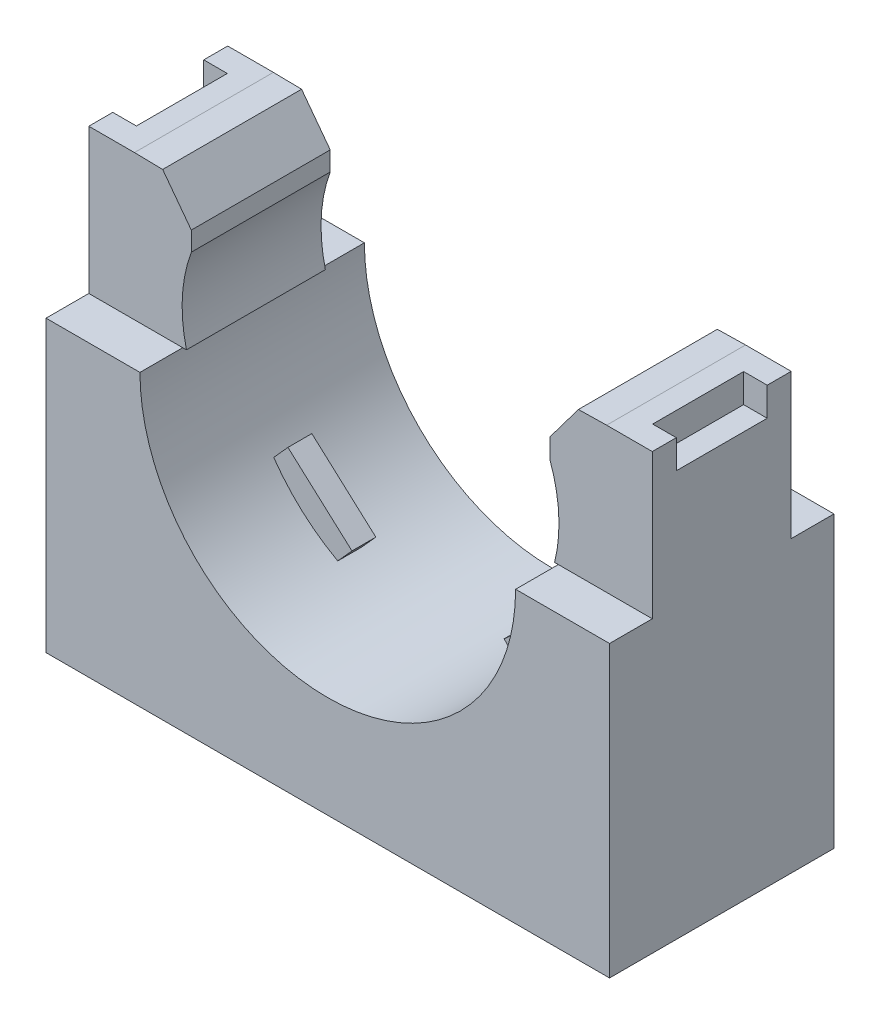
SolidWorks part; units mm, degrees
ref_plane "Front Plane" through (0, 0, 0) normal (0, 0, 1) x (1, 0, 0)
ref_plane "Top Plane" through (0, 0, 0) normal (0, 1, 0) x (1, 0, 0)
ref_plane "Right Plane" through (0, 0, 0) normal (1, 0, 0) x (0, 0, -1)
sketch "Sketch1" plane through (0, 0, 0) normal (0, 0, 1) x (1, 0, 0)
  line L0 (-14.986, -11.557) -> (14.986, 11.557) construction
  line L1 (-14.986, 11.557) -> (14.986, 11.557)
  line L2 (-14.986, 11.557) -> (-14.986, -11.557)
  line L3 (-14.986, -11.557) -> (14.986, -11.557)
  line L4 (14.986, 11.557) -> (14.986, -11.557)
  arc A0 (-9.7893, 1.8564) -> (9.7927, 1.8735) centre (0, 3.8523) ccw construction
  point P4 (0, 0)
  dimension "D3" = 15.4093
  dimension "D4" = 9.9907
  dimension "B" = 29.972
  dimension "C" = 23.114
extrude "Extrude1" add sketch "Sketch1" along normal blind 11.938
sketch "Sketch2" plane through (0, 0, 11.938) normal (0, 0, 1) x (1, 0, 0)
  line L1 (-9.9907, 3.8523) -> (-9.7909, 3.8523)
  line L2 (9.7909, 3.8523) -> (9.9907, 3.8523)
  line L3 (9.5329, 8.4799) -> (9.5329, 11.5041)
  line L4 (9.5329, 11.5041) -> (12.5571, 11.557)
  line L5 (14.986, 11.557) -> (-14.986, 11.557) construction
  line L6 (0, 0) -> (0, 22.8281) construction
  line L7 (-9.5329, 11.5041) -> (-12.5571, 11.557)
  line L8 (-9.5329, 8.4799) -> (-9.5329, 11.5041)
  line L9 (12.5571, 11.557) -> (-12.5571, 11.557)
  line L10 (14.986, -11.557) -> (14.986, 11.557) construction
  arc A0 (-9.9907, 3.8523) -> (9.9907, 3.8523) centre (0, 3.8523) ccw
  arc A1 (9.5329, 8.4799) -> (9.7909, 3.8523) centre (2.1566, 5.7478) cw
  arc A2 (-9.5329, 8.4799) -> (-9.7909, 3.8523) centre (-2.1566, 5.7478) ccw
  arc A3 (-9.7893, 1.8564) -> (9.7927, 1.8735) centre (0, 3.8523) ccw construction
  dimension "D1" = 0.1998
  dimension "D3" = 7.8661
  dimension "D2" = 3.0242
  dimension "D4" = 3.0242
  dimension "D7" = 5.4531
  dimension "D8" = 4.6276
extrude "Cut-Extrude1" cut sketch "Sketch2" against normal through all
sketch "Sketch3" plane through (0, 0, 0) normal (1, 0, 0) x (0, 0, -1)
  line L1 (-11.938, 3.8523) -> (-9.6634, 3.8523)
  line L2 (-9.6634, 11.557) -> (-9.6634, 3.8523)
  line L3 (-11.938, 3.8523) -> (-11.938, 11.557)
  line L4 (-2.2746, 11.557) -> (-2.2746, 3.8523)
  line L5 (-5.969, 31.6865) -> (-5.969, 10.4775) construction
  line L6 (-11.938, 11.557) -> (0, 11.557) construction
  line L7 (-11.938, -11.557) -> (-11.938, 11.557) construction
  line L8 (-11.938, 11.557) -> (-9.6634, 11.557)
  line L9 (0, 3.8523) -> (0, 11.557)
  line L10 (0, 3.8523) -> (-2.2746, 3.8523)
  line L11 (-2.2746, 11.557) -> (0, 11.557)
  line L13 (0, -11.557) -> (0, 11.557) construction
  dimension "D2" = 2.2746
extrude "Cut-Extrude2" cut sketch "Sketch3" against normal through all and the other way through all
sketch "Sketch4" plane through (0, -11.557, 0) normal (0, -1, 0) x (1, 0, 0)
  line L12 (-14.986, 11.1442) -> (14.986, 11.1442)
  line L13 (-14.1922, 11.1442) -> (14.1923, 11.1442)
  line L14 (-14.1922, 0.7937) -> (-14.1922, 11.938)
  line L15 (14.1923, 0.7937) -> (-14.1922, 0.7937)
  line L16 (14.1923, 11.938) -> (14.1923, 0.7937)
  line L17 (-14.1922, 0.7937) -> (-14.1922, 11.1442)
  line L18 (14.1923, 0.7937) -> (-14.1922, 0.7937)
  line L19 (14.1923, 11.1442) -> (14.1923, 0.7937)
  dimension "D1" = 0.7937
  dimension "D2" = 0.7937
extrude "Cut-Extrude3" cut sketch "Sketch4" against normal blind 0.254
sketch "Sketch5" plane through (0, 11.557, 0) normal (0, 1, 0) x (1, 0, 0)
  line L0 (-14.986, -2.2746) -> (-12.5571, -2.2746) construction
  line L2 (-14.986, -3.5503) -> (-13.7309, -3.5503)
  line L3 (-14.986, -3.5503) -> (-14.986, -8.3877)
  line L4 (-14.986, -8.3877) -> (-13.7309, -8.3877)
  line L6 (-13.7309, -3.5503) -> (-13.7309, -8.3877)
  line L10 (14.986, -3.5503) -> (13.7309, -3.5503)
  line L11 (14.986, -3.5503) -> (14.986, -8.3877)
  line L12 (14.986, -8.3877) -> (13.7309, -8.3877)
  line L13 (13.7309, -3.5503) -> (13.7309, -8.3877)
  line L14 (14.986, -9.6634) -> (14.986, -2.2746) construction
  line L15 (-14.986, -9.6634) -> (-14.986, -2.2746) construction
  line L16 (12.5571, -5.969) -> (-12.5571, -5.969) construction
  line L17 (12.5571, -2.2746) -> (12.5571, -9.6634) construction
  line L18 (-12.5571, -2.2746) -> (-12.5571, -9.6634) construction
  dimension "D1" = 1.2757
  dimension "D2" = 1.1737
extrude "Cut-Extrude4" cut sketch "Sketch5" against normal blind 1.524
ref_plane "Plane1" through (0, 0, 5.969) normal (0, 0, -1) x (-1, 0, 0)
sketch "Sketch6" plane through (0, 0, 5.969) normal (0, 0, -1) x (-1, 0, 0)
  line L0 (0, 0) -> (0, -34.0604) construction
  line L1 (2.54, -11.303) -> (0, -11.303)
  line L2 (14.1922, -11.303) -> (-14.1923, -11.303) construction
  line L3 (0, -6.223) -> (4.445, -6.223)
  line L4 (4.445, -6.223) -> (4.445, -8.763)
  line L5 (4.445, -8.763) -> (2.54, -8.763)
  line L6 (2.54, -8.763) -> (2.54, -11.303)
  line L7 (0, -11.303) -> (0, -6.223)
  dimension "E" = 8.89
  dimension "D" = 5.08
  dimension "D3" = 2.54
  dimension "D4" = 5.08
revolve "Cut-Revolve1" cut sketch "Sketch6" angle 360 about L0
sketch "Sketch7" plane through (0, 0, 5.969) normal (0, 0, -1) x (-1, 0, 0)
  line L0 (0, 16.5622) -> (0, -24.4387) construction
  line L1 (0, 3.8523) -> (5.7503, -2.534) construction
  line L2 (4.0476, -4.0672) -> (7.4531, -1.0009)
  line L3 (7.4531, -1.0009) -> (8.2096, -1.8411)
  line L4 (4.0476, -4.0672) -> (4.8041, -4.9075)
  line L5 (-4.0476, -4.0672) -> (-4.8041, -4.9075)
  line L6 (-7.4531, -1.0009) -> (-8.2096, -1.8411)
  line L7 (-4.0476, -4.0672) -> (-7.4531, -1.0009)
  arc A0 (-9.7927, 1.8735) -> (9.7893, 1.8564) centre (0, 3.8523) ccw construction
  arc A3 (4.8041, -4.9075) -> (8.2096, -1.8411) centre (0, 3.8523) ccw
  arc A4 (-4.8041, -4.9075) -> (-8.2096, -1.8411) centre (0, 3.8523) cw
  point P9 (5.7503, -2.534)
  dimension "D1" = 42
  dimension "D2" = 4.5826
  dimension "D3" = 1.1307
extrude "Extrude2" add sketch "Sketch7" along normal mid plane 1.27
sketch "Sketch8" plane through (0, 0, 9.6634) normal (0, 0, 1) x (1, 0, 0)
  line L0 (-9.5329, 11.5308) -> (-11.0569, 11.5308)
  line L1 (-9.5329, 11.5308) -> (-9.5329, 9.4988)
  line L2 (-9.5329, 11.5041) -> (-9.5329, 8.4799) construction
  line L3 (-9.5329, 9.4988) -> (-11.0569, 11.5308)
  line L4 (0, 0) -> (0, -13.7082) construction
  line L5 (-12.5571, 11.557) -> (-9.5329, 11.5041) construction
  line L6 (0, 0) -> (0, -34.0604) construction
  line L7 (9.5329, 11.5308) -> (11.0569, 11.5308)
  line L8 (9.5329, 11.5308) -> (9.5329, 9.4988)
  line L9 (9.5329, 9.4988) -> (11.0569, 11.5308)
  dimension "D1" = 1.524
  dimension "D2" = 2.032
extrude "Cut-Extrude5" cut sketch "Sketch8" against normal through all
equation "\"D3@Sketch1\" = (\"C@Sketch1\"/3)*2"
equation "\"D4@Sketch1\" = \"B@Sketch1\"/3"
equation "\"D3@Sketch2\" = ((\"D4@Sketch1\"/4)*3)+0.0146875"
equation "\"D8@Sketch2\" = (\"D3@Sketch2\"/2)+0.02734375"
equation "\"D4@Sketch2\" = ((\"D8@Sketch2\"/4)*3)-0.009765625-0.0078125"
equation "\"D7@Sketch2\" = (\"D4@Sketch2\"*2)-0.0234375"
equation "\"D2@Sketch7\" = (\"D4@Sketch1\"/2)-0.01625"
equation "\"D3@Sketch7\" = \"D2@Sketch7\"/3-0.015625"
equation "\"D2@Sketch2\" = \"D4@Sketch2\""
equation "\"D1@Sketch2\" = \"D4@Sketch1\"/50"
equation "\"D4@Sketch6\" = \"D@Sketch6\""
equation "\"D3@Sketch6\" = \"D4@Sketch6\"/2"
